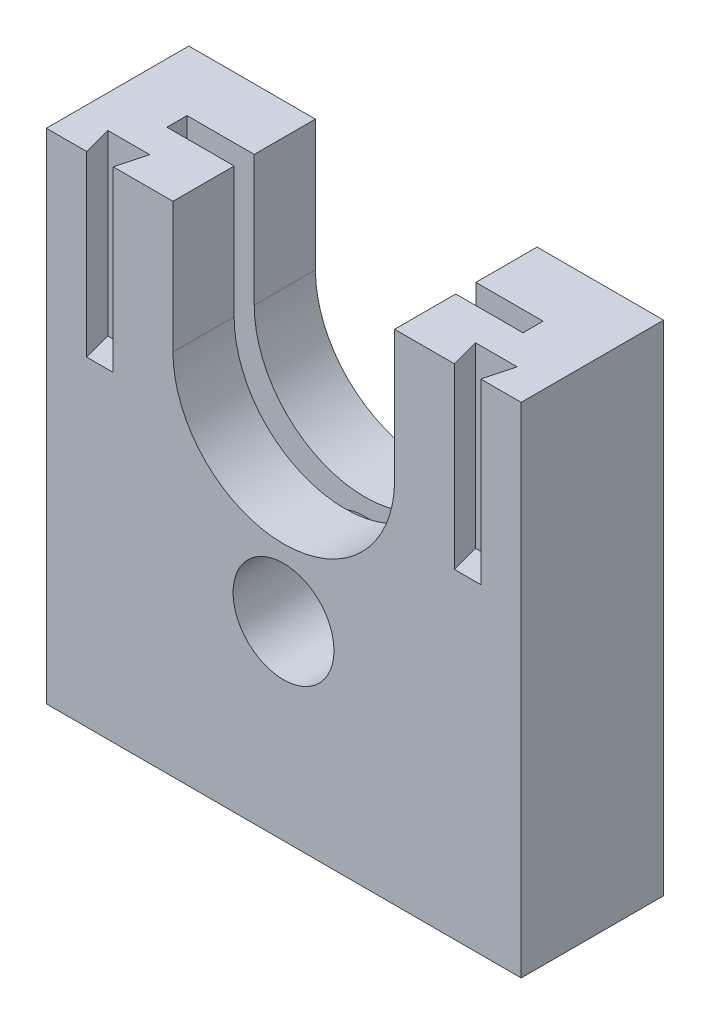
SolidWorks part; units mm, degrees
ref_plane "Front Plane" through (0, 0, 0) normal (0, 0, 1) x (1, 0, 0)
ref_plane "Top Plane" through (0, 0, 0) normal (0, 1, 0) x (1, 0, 0)
ref_plane "Right Plane" through (0, 0, 0) normal (1, 0, 0) x (0, 0, -1)
sketch "Sketch2" plane through (0, 0, 0) normal (0, 0, 1) x (1, 0, 0)
  line L1 (-19.4872, 32.4615) -> (16.5128, 32.4615)
  line L2 (-19.4872, 32.4615) -> (-19.4872, -9.5385)
  line L3 (-19.4872, -9.5385) -> (16.5128, -9.5385)
  line L4 (16.5128, 32.4615) -> (16.5128, -9.5385)
  dimension "D1" = 36
  dimension "D2" = 42
extrude "Boss-Extrude1" add sketch "Sketch2" along normal blind 12
sketch "Sketch3" plane through (0, 32.4615, 0) normal (0, 1, 0) x (1, 0, 0)
  line L6 (-19.4872, -12) -> (-18.0872, -12) construction
  line L7 (16.5128, -12) -> (-19.4872, -12) construction
  line L8 (-18.0872, -12) -> (-18.737, -9.575)
  line L9 (-18.737, -9.575) -> (-15.2124, -9.575)
  line L10 (-15.2124, -9.575) -> (-15.8622, -12)
  line L16 (16.5128, -12) -> (15.1128, -12) construction
  line L17 (15.1128, -12) -> (15.7626, -9.575)
  line L18 (15.7626, -9.575) -> (12.238, -9.575)
  line L19 (12.238, -9.575) -> (12.8878, -12)
  line L21 (-18.0872, -12) -> (-15.8622, -12)
  line L23 (15.1128, -12) -> (12.8878, -12)
  dimension "D7" = 1.4
  dimension "D8" = 2.425
  dimension "D9" = 105
  dimension "D10" = 105
  dimension "D11" = 2.225
  dimension "D17" = 1.4
  dimension "D18" = 2.425
  dimension "D19" = 2.225
  dimension "D20" = 105
  dimension "D21" = 105
ref_plane "Plane1" through (0, 0, 8) normal (0, 0, 1) x (1, 0, 0)
extrude "Cut-Extrude1" cut sketch "Sketch3" against normal blind 15
sketch "Sketch4" plane through (0, 0, 12) normal (0, 0, 1) x (1, 0, 0)
  line L0 (-15.8622, 32.4615) -> (12.8878, 32.4615) construction
  line L1 (-10.8235, 32.4615) -> (7.8491, 32.4615)
  line L2 (-19.4872, -9.5385) -> (16.5128, -9.5385) construction
  line L5 (7.8491, 21.4615) -> (7.8491, 32.4615)
  line L6 (-1.4872, -9.5385) -> (-1.4872, 32.4615) construction
  line L7 (-10.8235, 21.4615) -> (-10.8235, 32.4615)
  arc A1 (-10.8235, 21.4615) -> (7.8491, 21.4615) centre (-1.4872, 21.4615) ccw
  dimension "D1" = 11
extrude "Cut-Extrude2" cut sketch "Sketch4" against normal blind 12
sketch "Sketch5" plane through (0, 32.4615, 0) normal (0, 1, 0) x (1, 0, 0)
  line L0 (-19.4872, -12) -> (-19.4872, 0) construction
  line L5 (-19.4872, -6) -> (16.5128, -6) construction
  line L6 (16.5128, -12) -> (16.5128, 0) construction
  line L7 (-19.4872, 0) -> (16.5128, -12) construction
  line L9 (-16.4872, -6.8477) -> (13.5128, -6.8477)
  line L10 (-16.4872, -6.8477) -> (-16.4872, -5.1523)
  line L11 (-16.4872, -5.1523) -> (13.5128, -5.1523)
  line L12 (13.5128, -6.8477) -> (13.5128, -5.1523)
  line L13 (-16.4872, -6.8477) -> (13.5128, -5.1523) construction
  line L14 (-16.4872, -5.1523) -> (13.5128, -6.8477) construction
  point P0 (-1.4872, -6)
  dimension "D1" = 30
extrude "Cut-Extrude3" cut sketch "Sketch5" against normal blind 25
sketch "Sketch6" plane through (0, 0, 12) normal (0, 0, 1) x (1, 0, 0)
  circle A0 centre (-1.5094, 6.4615) radius 4.25
  dimension "D1" = 8.5
extrude "Cut-Extrude4" cut sketch "Sketch6" against normal blind 7.1
sketch "Sketch7" plane through (0, 32.4615, 0) normal (0, 1, 0) x (1, 0, 0)
  line L1 (-19.4872, 0) -> (-21.4872, 0)
  line L2 (-19.4872, 0) -> (-19.4872, -12)
  line L3 (-19.4872, -12) -> (-21.4872, -12)
  line L4 (-21.4872, 0) -> (-21.4872, -12)
  line L9 (16.5128, 0) -> (16.5128, -12)
  line L10 (16.5128, 0) -> (18.5128, 0)
  line L11 (16.5128, -12) -> (18.5128, -12)
  line L12 (18.5128, 0) -> (18.5128, -12)
  dimension "D1" = 12
  dimension "D2" = 2
  dimension "D3" = 2
extrude "Boss-Extrude2" add sketch "Sketch7" against normal blind 42
